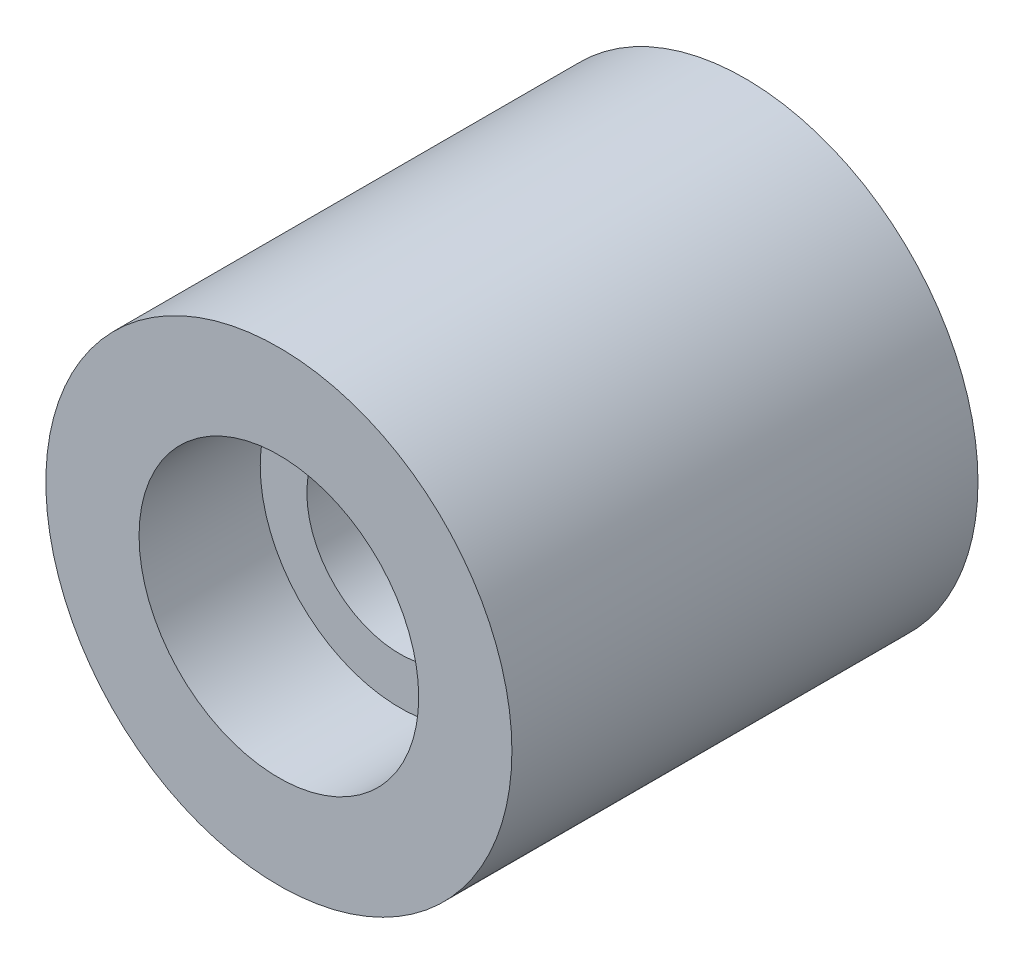
SolidWorks part; units mm, degrees
material "1.7223 (41CrMo4)"
ref_plane "Alzado" through (0, 0, 0) normal (0, 0, 1) x (1, 0, 0)
ref_plane "Planta" through (0, 0, 0) normal (0, 1, 0) x (1, 0, 0)
ref_plane "Vista lateral" through (0, 0, 0) normal (1, 0, 0) x (0, 0, -1)
sketch "Croquis2" plane through (0, 0, 0) normal (0, 1, 0) x (1, 0, 0)
  line L0 (0, 0) -> (0, 5) construction
  line L1 (-1.5, 0) -> (-2.5, 0)
  line L2 (-2.5, 0) -> (-2.5, 5)
  line L3 (-2.5, 5) -> (-1, 5)
  line L4 (-1.5, 0) -> (-1.5, 1.3)
  line L6 (-2, 1.8) -> (-2, 4.5)
  line L7 (-2, 4.5) -> (-1, 4.5)
  line L10 (-2, 1.8) -> (-1, 1.8)
  line L12 (-1.5, 1.3) -> (-1, 1.3)
  line L13 (-1, 1.8) -> (-1, 1.3)
  line L17 (-1, 5) -> (-1, 4.5)
  point P17 (-2, 0)
  dimension "D1" = 3
  dimension "D2" = 5
  dimension "D3" = 5
  dimension "D4" = 1.8
  dimension "D5" = 4
  dimension "D6" = 0.5
  dimension "D7" = 0.5
revolve "Revolución1" add sketch "Croquis2" angle 360 about L0
